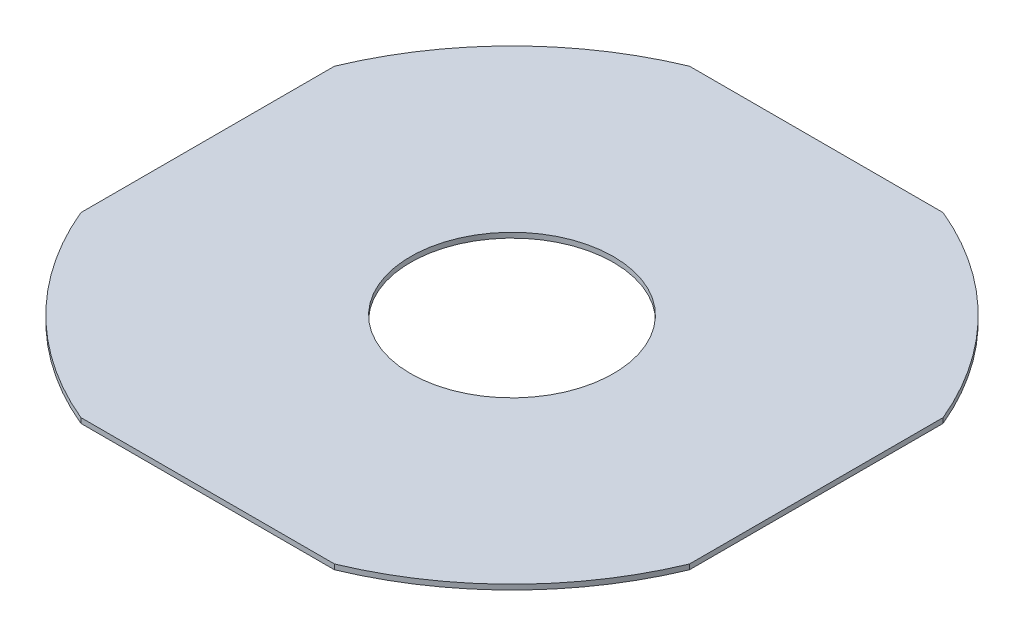
SolidWorks part; units mm, degrees
material "6061-T4 (SS)"
ref_plane "Front Plane" through (0, 0, 0) normal (0, 0, 1) x (1, 0, 0)
ref_plane "Top Plane" through (0, 0, 0) normal (0, 1, 0) x (1, 0, 0)
ref_plane "Right Plane" through (0, 0, 0) normal (1, 0, 0) x (0, 0, -1)
sketch "Sketch1" plane through (0, 0, 0) normal (0, 1, 0) x (1, 0, 0)
  line L1 (-600, -600) -> (600, -600)
  line L2 (-600, -600) -> (-600, 600)
  line L3 (-600, 600) -> (600, 600)
  line L4 (600, -600) -> (600, 600)
  line L5 (-600, -600) -> (600, 600) construction
  line L6 (-600, 600) -> (600, -600) construction
  point P0 (0, 0)
  dimension "D1" = 1200
  dimension "D2" = 1200
extrude "Boss-Extrude1" add sketch "Sketch1" along normal blind 10
sketch "Sketch2" plane through (0, 10, 0) normal (0, 1, 0) x (1, 0, 0)
  circle A0 centre (0, 0) radius 200
  dimension "D1" = 400
extrude "Cut-Extrude1" cut sketch "Sketch2" against normal through all
sketch "Sketch3" plane through (0, 10, 0) normal (0, 1, 0) x (1, 0, 0)
  circle A0 centre (0, 0) radius 650
  circle A1 centre (0, 0) radius 1053.6231
extrude "Cut-Extrude2" cut sketch "Sketch3" against normal through all
